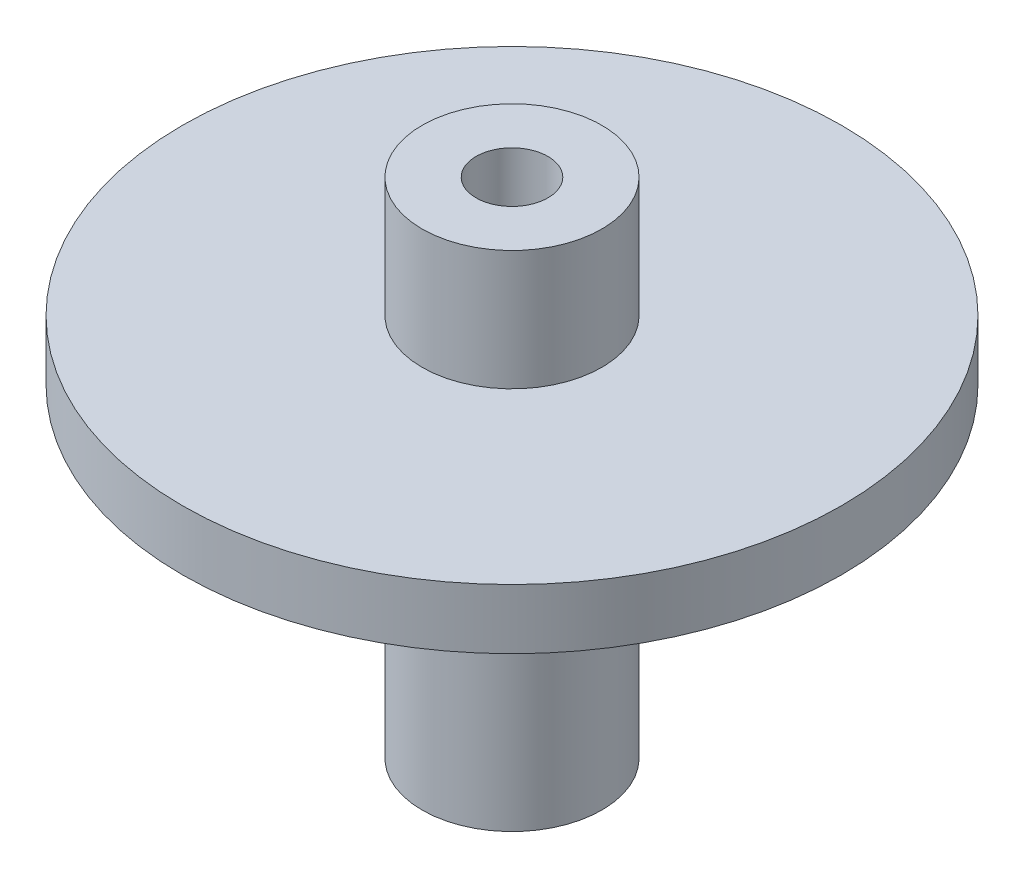
SolidWorks part; units mm, degrees
material "1.0037 (S235JR)"
ref_plane "Vorne" through (0, 0, 0) normal (0, 0, 1) x (1, 0, 0)
ref_plane "Oben" through (0, 0, 0) normal (0, 1, 0) x (1, 0, 0)
ref_plane "Rechts" through (0, 0, 0) normal (1, 0, 0) x (0, 0, -1)
sketch "Skizze1" plane through (0, 0, 0) normal (1, 0, 0) x (0, 0, -1)
  line L0 (0, 21.6854) -> (0, 0) construction
  line L1 (-3, 0) -> (-27.5, 0)
  line L2 (-27.5, 0) -> (-27.5, -5)
  line L3 (-27.5, -5) -> (-7.5, -5)
  line L4 (-7.5, -5) -> (-7.5, -32)
  line L5 (-7.5, -32) -> (-3, -32)
  line L7 (-3, 0) -> (-3, -32)
  line L8 (0, -32) -> (0, -33.0857) construction
  dimension "D1" = 5
  dimension "D2" = 27
  dimension "D3" = 55
  dimension "D4" = 15
  dimension "D5" = 6
revolve "Rotation1" add sketch "Skizze1" angle 360 about L0
sketch "Skizze2" plane through (0, 0, 0) normal (0, 1, 0) x (1, 0, 0)
  circle A0 centre (0, 0) radius 7.5
  circle A1 centre (0, 0) radius 3
  dimension "D1" = 15
extrude "Aufsatz-Linear austragen1" add sketch "Skizze2" along normal blind 10
